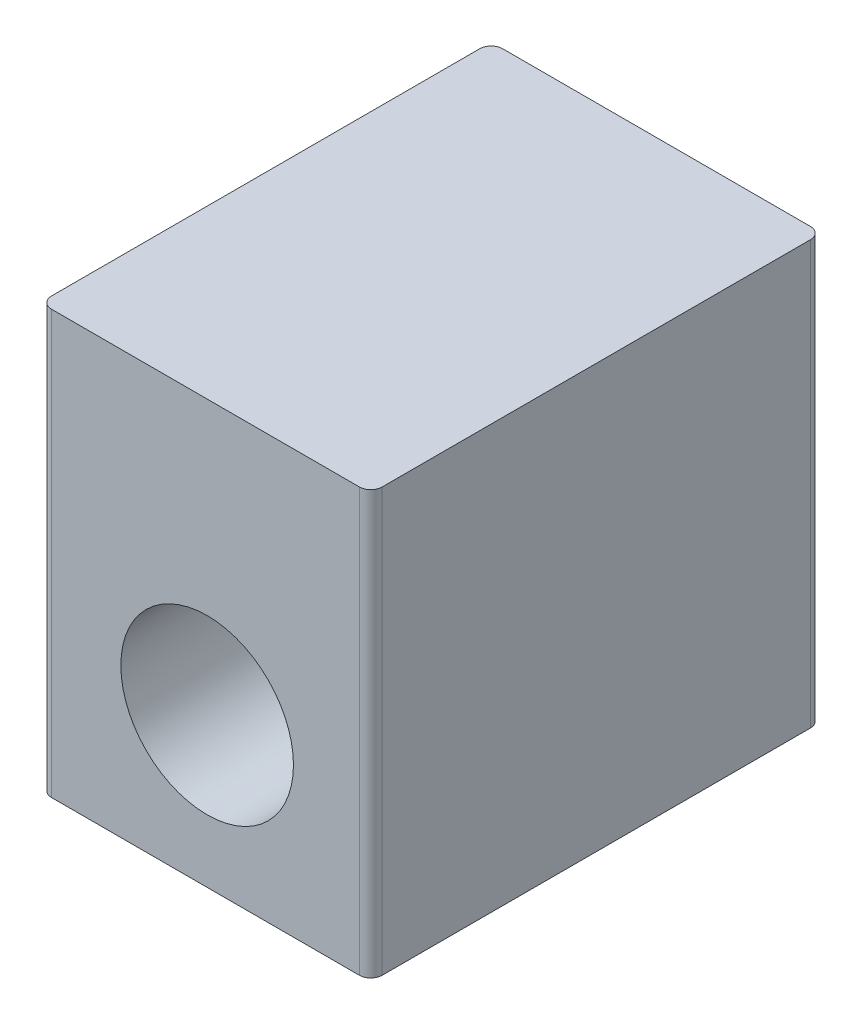
SolidWorks part; units mm, degrees
material "6061 Alloy"
ref_plane "Front Plane" through (0, 0, 0) normal (0, 0, 1) x (1, 0, 0)
ref_plane "Top Plane" through (0, 0, 0) normal (0, 1, 0) x (1, 0, 0)
ref_plane "Right Plane" through (0, 0, 0) normal (1, 0, 0) x (0, 0, -1)
sketch "Sketch1" plane through (0, 0, 0) normal (0, 1, 0) x (1, 0, 0)
  line L1 (0, 0) -> (22.0472, 0)
  line L2 (0, 0) -> (0, 30.0736)
  line L3 (0, 30.0736) -> (22.0472, 30.0736)
  line L4 (22.0472, 0) -> (22.0472, 30.0736)
  dimension "D1" = 22.0472
  dimension "D2" = 30.0736
extrude "Boss-Extrude1" add sketch "Sketch1" along normal blind 28.194
sketch "Sketch2" plane through (0, 0, 0) normal (0, -1, 0) x (1, 0, 0)
  line L0 (0, -5.2705) -> (22.0472, -5.2705) construction
  line L1 (0, -30.0736) -> (0, 0) construction
  line L2 (22.0472, 0) -> (22.0472, -30.0736) construction
  line L3 (0, 0) -> (22.0472, 0) construction
  circle A0 centre (3.2131, -5.2705) radius 1.5875
  circle A1 centre (18.7071, -5.2705) radius 1.5875
  dimension "D1" = 3.175
  dimension "D2" = 5.2705
  dimension "D3" = 3.2131
  dimension "D4" = 3.3401
extrude "Cut-Extrude1" cut sketch "Sketch2" against normal blind 4.826
sketch "Sketch3" plane through (0, 0, 0) normal (0, 0, 1) x (1, 0, 0)
  line L1 (0, 0) -> (22.0472, 0) construction
  line L2 (22.0472, 28.194) -> (22.0472, 0) construction
  circle A0 centre (11.1379, 9.9441) radius 5.7531
  dimension "D1" = 11.5062
  dimension "D2" = 9.9441
  dimension "D3" = 10.9093
extrude "Cut-Extrude2" cut sketch "Sketch3" against normal blind 13.462
sketch "Sketch4" plane through (0, 0, -30.0736) normal (0, 0, -1) x (-1, 0, 0)
  line L0 (-22.0472, 0) -> (0, 0) construction
  line L1 (-22.0472, 28.194) -> (-22.0472, 0) construction
  circle A0 centre (-10.9093, 9.7917) radius 5.7531
  dimension "D1" = 11.5062
  dimension "D2" = 9.7917
  dimension "D3" = 11.1379
extrude "Cut-Extrude3" cut sketch "Sketch4" against normal blind 13.462
fillet "Fillet1" radius 0.762 4 edges at (0, 14.097, -30.0736) (22.0472, 14.097, -30.0736) (22.0472, 14.097, 0) (0, 14.097, 0)
